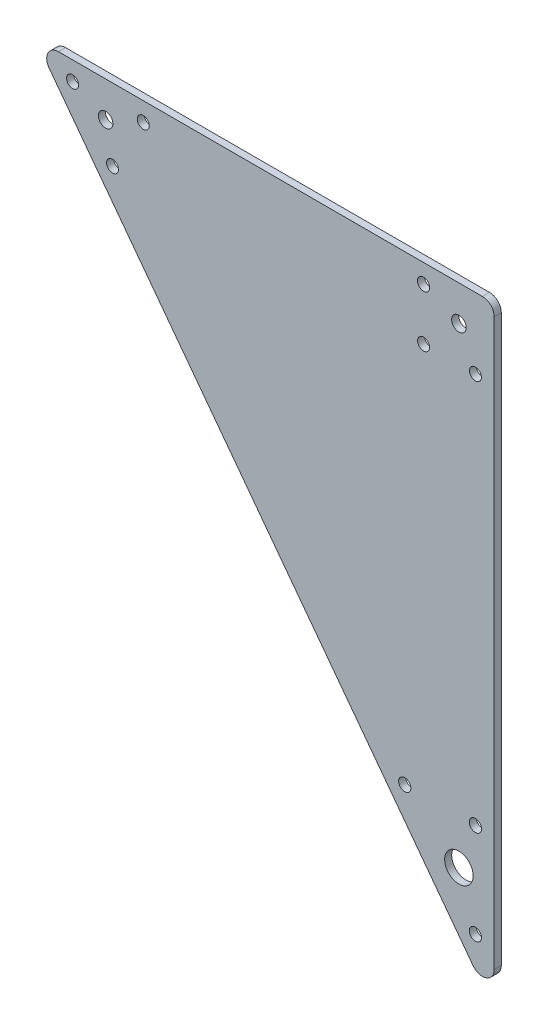
SolidWorks part; units mm, degrees
material "6061 合金"
ref_plane "前视基准面" through (0, 0, 0) normal (0, 0, 1) x (1, 0, 0)
ref_plane "上视基准面" through (0, 0, 0) normal (0, 1, 0) x (1, 0, 0)
ref_plane "右视基准面" through (0, 0, 0) normal (1, 0, 0) x (0, 0, -1)
sketch "草图2" plane through (0, 0, 0) normal (0, 0, 1) x (1, 0, 0)
  line L3 (-180, 15) -> (15, 15)
  line L4 (15, 15) -> (15, -245)
  line L6 (-180, 15) -> (15, -245)
  line L7 (-150, 0) -> (0, 0) construction
  line L8 (0, 0) -> (0, -200) construction
  line L9 (-150, 0) -> (0, -200) construction
  line L10 (-164, 7) -> (-147.0489, -15.6014) construction
  line L11 (-147.0489, -15.6014) -> (-134, 7) construction
  line L12 (-134, 7) -> (-164, 7) construction
  line L13 (-23, -181) -> (7, -221) construction
  line L14 (-15, 7) -> (7, 7) construction
  line L17 (7, 7) -> (7, -15) construction
  line L18 (7, -221) -> (7, -181) construction
  line L19 (7, -181) -> (-23, -181) construction
  line L20 (7, -15) -> (-15, -15) construction
  line L21 (-15, -15) -> (-15, 7) construction
  circle A0 centre (0, 0) radius 3.1
  circle A1 centre (-150, 0) radius 3.1
  circle A2 centre (0, -200) radius 6.05
  circle A7 centre (-164, 7) radius 2.55
  circle A8 centre (-134, 7) radius 2.55
  circle A9 centre (-147.0489, -15.6014) radius 2.55
  circle A10 centre (-15, 7) radius 2.6
  circle A12 centre (7, -15) radius 2.55
  circle A13 centre (7, -221) radius 2.6
  circle A14 centre (-23, -181) radius 2.6
  circle A15 centre (7, -181) radius 2.6
  circle A18 centre (-15, -15) radius 2.55
  dimension "D1" = 200
  dimension "D2" = 150
  dimension "D3" = 15
  dimension "D5" = 8
  dimension "D7" = 8
  dimension "D8" = 12.1
  dimension "D16" = 40
  dimension "D17" = 5.2
  dimension "D18" = 6.2
  dimension "D4" = 15
  dimension "D6" = 15
  dimension "D9" = 30
  dimension "D10" = 8
  dimension "D11" = 8
  dimension "D12" = 22
  dimension "D13" = 22
  dimension "D14" = 8
  dimension "D15" = 8
  dimension "D19" = 60
extrude "凸台-拉伸1" add sketch "草图2" along normal blind 3
fillet "圆角1" radius 5 3 edges at (15, -245, 1.5) (-180, 15, 1.5) (15, 15, 1.5)
